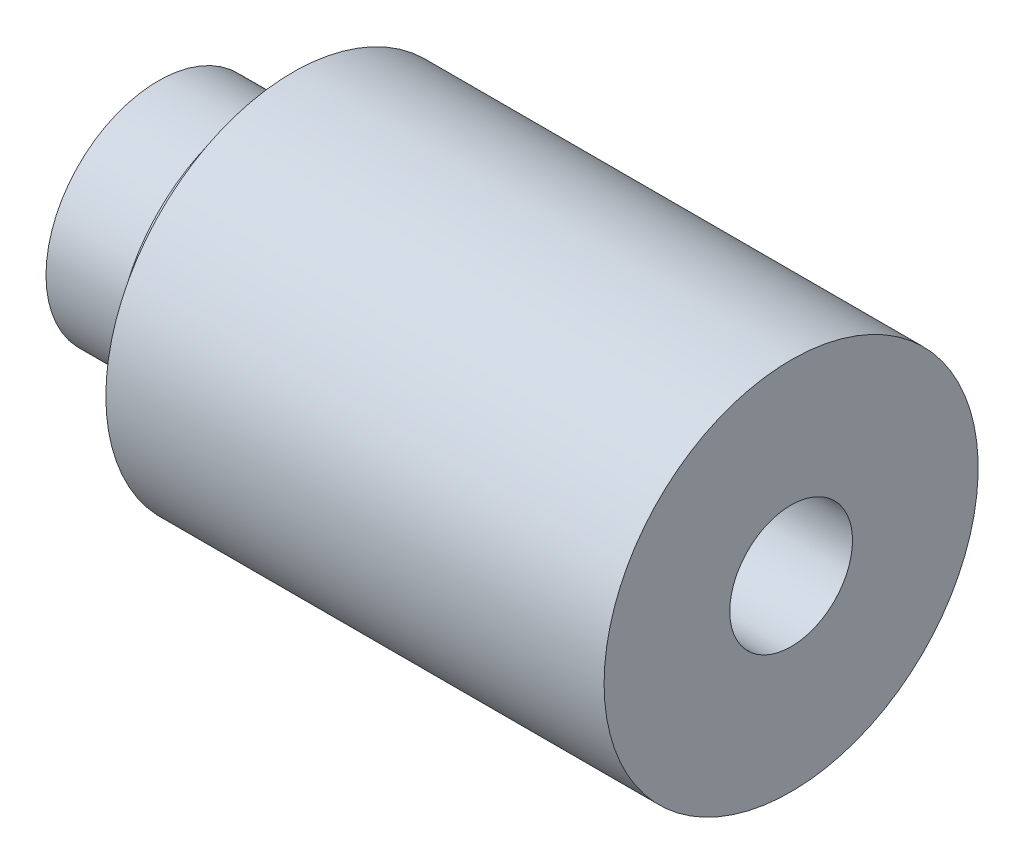
SolidWorks part; units mm, degrees
material "AISI 1020"
ref_plane "Спереди" through (0, 0, 0) normal (0, 0, 1) x (1, 0, 0)
ref_plane "Сверху" through (0, 0, 0) normal (0, 1, 0) x (1, 0, 0)
ref_plane "Справа" through (0, 0, 0) normal (1, 0, 0) x (0, 0, -1)
sketch "Эскиз1" plane through (0, 0, 0) normal (0, 0, 1) x (1, 0, 0)
  line L0 (-1000, 0) -> (49000, 0) construction
  line L1 (1.2, 0) -> (1.2, 7.5)
  line L2 (1.2, 7.5) -> (8.2, 7.5)
  line L3 (8.2, 14) -> (8.2, -14) construction
  line L4 (8.2, 7.5) -> (8.2, 9.8333)
  line L5 (8.2, 9.8333) -> (10.2, 9.8333)
  line L6 (43.5, 12.5) -> (43.5, 0)
  line L7 (43.5, 0) -> (1.2, 0)
  line L8 (7.7, 7.5) -> (1.7, 7.5) construction
  line L9 (1.2, 9.8333) -> (1.2, -9.8333) construction
  line L11 (10.2, 9.8333) -> (10.2, 12.5)
  line L12 (10.2, 12.5) -> (43.5, 12.5)
  line L13 (18.5, -16) -> (18.5, 16) construction
  dimension "D1" = 25
  dimension "D2" = 2
  dimension "D3" = 25
revolve "Повернуть1" add sketch "Эскиз1" angle 360 about L0
hole_wizard "Диаметр отверстия Ø8.2 (8.2)1" positions "Эскиз2" profile "Эскиз3" hole size "Ø8.2" standard "ISO" end condition through all
sketch "Эскиз2" plane through (1.2, 0, 0) normal (-1, 0, 0) x (0, 0, 1)
  point P0 (0, 0)
sketch "Эскиз3" plane through (1.2, 0, 0) normal (0, 1, 0) x (0, 0, 1)
  line L0 (0, 0) -> (0, 42.3)
  line L1 (0, 42.3) -> (4.1, 42.3)
  line L2 (4.1, 42.3) -> (4.1, 0)
  line L5 (4.1, 0) -> (0, 0)
  line L11 (0, -6.35) -> (0, 107.95) construction
  dimension "Диаметр сквозного отверстия" = 8.2
  dimension "Глубина сквозного отверстия" = 42.3
